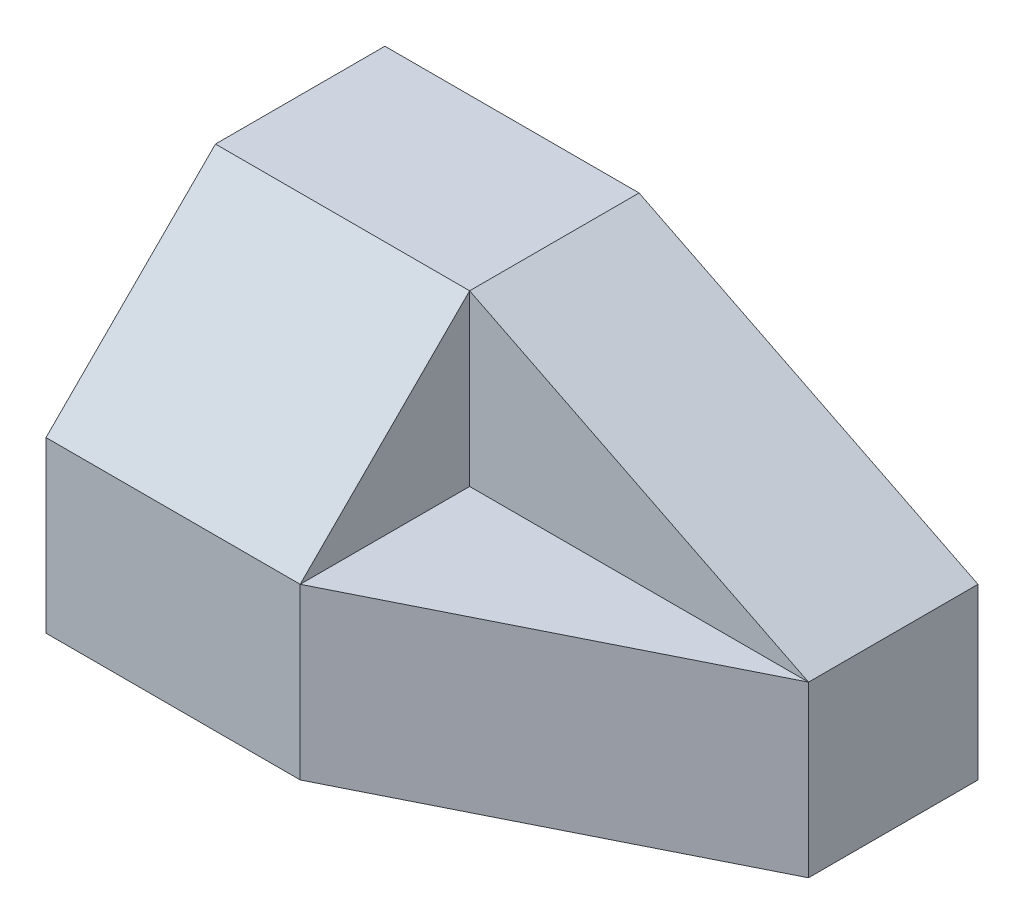
SolidWorks part; units mm, degrees
ref_plane "前基準面" through (0, 0, 0) normal (0, 0, 1) x (1, 0, 0)
ref_plane "上基準面" through (0, 0, 0) normal (0, 1, 0) x (1, 0, 0)
ref_plane "右基準面" through (0, 0, 0) normal (1, 0, 0) x (0, 0, -1)
sketch "草圖1" plane through (0, 0, 0) normal (0, 1, 0) x (1, 0, 0)
  line L1 (-3.5, -2) -> (3.5, -2)
  line L2 (-3.5, -2) -> (-3.5, 2)
  line L3 (-3.5, 2) -> (3.5, 2)
  line L4 (3.5, -2) -> (3.5, 2)
  line L5 (-3.5, -2) -> (3.5, 2) construction
  line L6 (-3.5, 2) -> (3.5, -2) construction
  point P0 (0, 0)
  dimension "D1" = 7
  dimension "D2" = 4
extrude "填料-伸長1" add sketch "草圖1" along normal blind 4
sketch "草圖2" plane through (0, 0, 2) normal (0, 0, 1) x (1, 0, 0)
  line L0 (3.5, 4) -> (-0.5, 4)
  line L1 (-3.5, 4) -> (3.5, 4) construction
  line L2 (-0.5, 4) -> (3.5, 2)
  line L3 (3.5, 4) -> (3.5, 0) construction
  line L4 (3.5, 2) -> (3.5, 4)
  dimension "D1" = 4
  dimension "D2" = 2
extrude "除料-伸長1" cut sketch "草圖2" against normal blind 4
sketch "草圖3" plane through (0, 0, 0) normal (0, 1, 0) x (1, 0, 0)
  line L0 (-0.5, -2) -> (3.5, -2)
  line L1 (-0.5, -2) -> (3.5, -2) construction
  line L2 (3.5, -2) -> (3.5, 0)
  line L3 (3.5, 2) -> (3.5, -2) construction
  line L4 (3.5, 0) -> (-0.5, -2)
  dimension "D1" = 4
  dimension "D2" = 2
extrude "除料-伸長2" cut sketch "草圖3" along normal blind 6.4 contours L4 L0 L2
sketch "草圖4" plane through (0, 4, 0) normal (0, 1, 0) x (1, 0, 0)
  line L0 (3.5, 0) -> (-0.5, 0)
  line L1 (-0.5, 2) -> (-0.5, -2) construction
  line L2 (-0.5, 0) -> (-0.5, -2)
  line L3 (-0.5, -2) -> (3.5, 0)
extrude "除料-伸長3" cut sketch "草圖4" against normal blind 2
sketch "草圖5" plane through (-0.5, 0, 0) normal (1, 0, 0) x (0, 0, -1)
  line L0 (0, 4) -> (-2, 4)
  line L1 (-2, 4) -> (-2, 2)
  line L2 (-2, 2) -> (0, 4)
extrude "除料-伸長4" cut sketch "草圖5" against normal blind 3.8
